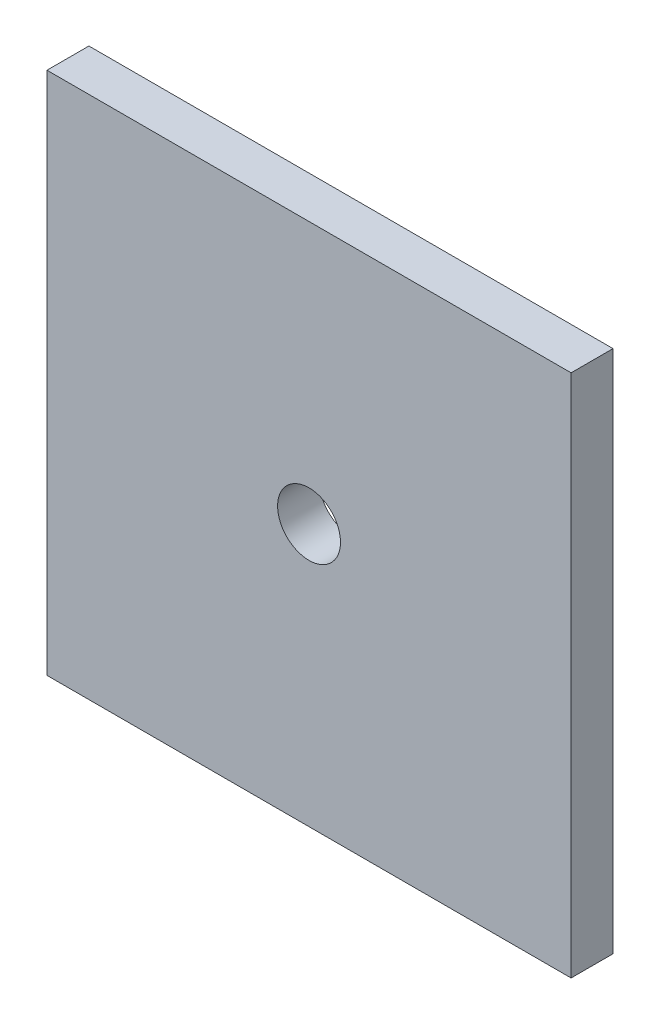
SolidWorks part; units mm, degrees
ref_plane "Plan de face" through (0, 0, 0) normal (0, 0, 1) x (1, 0, 0)
ref_plane "Plan de dessus" through (0, 0, 0) normal (0, 1, 0) x (1, 0, 0)
ref_plane "Plan de droite" through (0, 0, 0) normal (1, 0, 0) x (0, 0, -1)
sketch "Sketch1" plane through (0, 0, 0) normal (0, 0, 1) x (1, 0, 0)
  line L1 (0, 0) -> (50, 0)
  line L2 (0, 0) -> (0, 50)
  line L3 (0, 50) -> (50, 50)
  line L4 (50, 0) -> (50, 50)
  dimension "D1" = 50
  dimension "D2" = 50
extrude "Boss-Extrude1" add sketch "Sketch1" along normal blind 4
sketch "Sketch3" plane through (0, 0, 4) normal (0, 0, 1) x (1, 0, 0)
  line L0 (50, 50) -> (0, 0) construction
  circle A0 centre (25, 25) radius 3
  dimension "D1" = 6
extrude "Cut-Extrude1" cut sketch "Sketch3" against normal up to surface (4 mm away) contours A0 up to face at (25, 25, 0)
